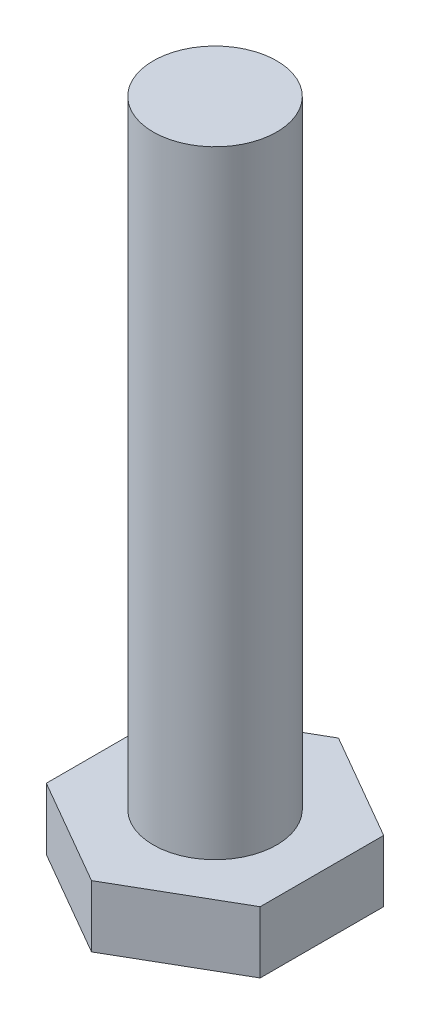
SolidWorks part; units mm, degrees
ref_plane "Front Plane" through (0, 0, 0) normal (0, 0, 1) x (1, 0, 0)
ref_plane "Top Plane" through (0, 0, 0) normal (0, 1, 0) x (1, 0, 0)
ref_plane "Right Plane" through (0, 0, 0) normal (1, 0, 0) x (0, 0, -1)
sketch "Sketch1" plane through (0, 0, 0) normal (0, 1, 0) x (1, 0, 0)
  circle A0 centre (0, 0) radius 1
  dimension "D1" = 2
extrude "Boss-Extrude1" add sketch "Sketch1" along normal blind 0.5
ref_plane "Plane1" through (0, 0.5, 0) normal (0, 1, 0) x (1, 0, 0)
sketch "Sketch2" plane through (0, 0.5, 0) normal (0, 1, 0) x (1, 0, 0)
  circle A0 centre (0, 0) radius 0.5
extrude "Boss-Extrude2" add sketch "Sketch2" along normal blind 5
ref_plane "Plane2" through (0, 0, 0) normal (0, -1, 0) x (-1, 0, 0)
sketch "Sketch3" plane through (0, 0, 0) normal (0, -1, 0) x (-1, 0, 0)
  line L0 (0, 1) -> (0, 0)
  line L1 (0, 0) -> (0.866, 0.5)
  line L2 (0.866, 0.5) -> (0, 1)
  line L3 (0.866, -0.5) -> (0.866, 0.5)
  line L4 (0, -1) -> (0.866, -0.5)
  line L5 (-0.866, -0.5) -> (0, -1)
  line L6 (-0.866, 0.5) -> (-0.866, -0.5)
  line L7 (0, 1) -> (-0.866, 0.5)
  circle A0 centre (0, 0) radius 1 construction
  point P18 (0, 0)
  dimension "D1" = 6
extrude "Cut-Extrude2" cut sketch "Sketch3" against normal blind 10 flip side to cut contours L1 L2 L0 | L0 L7 L6 L5 L4 L3 L1
